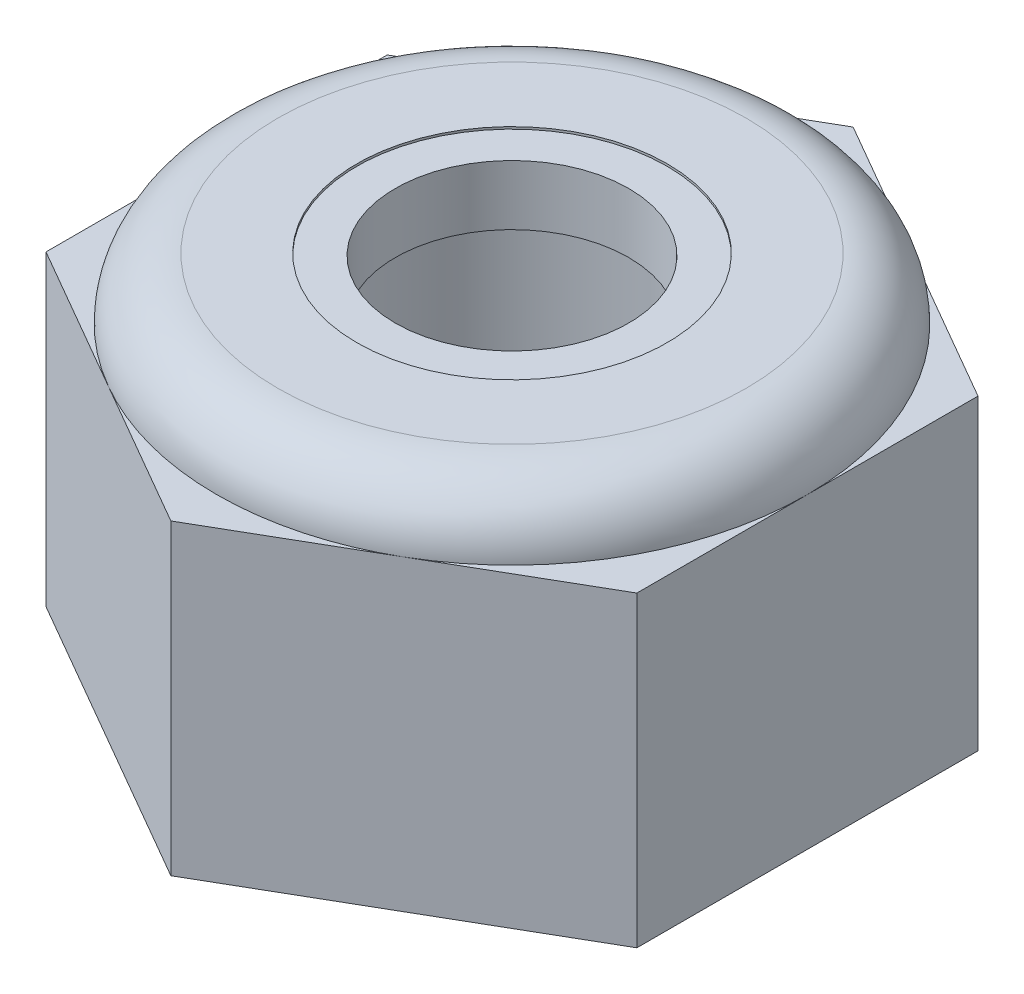
SolidWorks part; units mm, degrees
ref_plane "Front Plane" through (0, 0, 0) normal (0, 0, 1) x (1, 0, 0)
ref_plane "Top Plane" through (0, 0, 0) normal (0, 1, 0) x (1, 0, 0)
ref_plane "Right Plane" through (0, 0, 0) normal (1, 0, 0) x (0, 0, -1)
sketch "Sketch1" plane through (0, 0, 0) normal (0, 1, 0) x (1, 0, 0)
  line L1 (-4, -2.3094) -> (0, -4.6188)
  line L2 (0, -4.6188) -> (4, -2.3094)
  line L3 (4, -2.3094) -> (4, 2.3094)
  line L4 (4, 2.3094) -> (0, 4.6188)
  line L5 (0, 4.6188) -> (-4, 2.3094)
  line L6 (-4, 2.3094) -> (-4, -2.3094)
  line L7 (0, -55) -> (0, 55) construction
  circle A0 centre (0, 0) radius 4 construction
  dimension "D2" = 8
  dimension "D1" = 0
extrude "Boss-Extrude1" add sketch "Sketch1" along normal blind 4.16
sketch "Sketch3" plane through (0, 0, 0) normal (0, 0, 1) x (1, 0, 0)
  line L1 (3.17, 4.99) -> (0, 4.99)
  line L2 (0, 4.99) -> (0, 4.16)
  line L3 (0, 4.16) -> (4, 4.16)
  arc A0 (4, 4.16) -> (3.17, 4.99) centre (3.17, 4.16) ccw
  dimension "D2" = 0.83
  dimension "D1" = 0.83
revolve "Revolve1" add sketch "Sketch3" angle 360 about L2
hole_wizard "Tap Drill for M5x0.8 Tap1" positions "Sketch6" profile "Sketch7" hole size "M5x0.8" standard "ANSI Metric" end condition through all
sketch "Sketch6" plane through (0, 0, 0) normal (0, -1, 0) x (-1, 0, 0)
  point P0 (0, 0)
sketch "Sketch7" plane through (0, 0, 0) normal (1, 0, 0) x (0, 0, -1)
  line L0 (0, 0) -> (0, 4.99)
  line L1 (0, 4.99) -> (2.1, 4.99)
  line L2 (2.1, 4.99) -> (2.1, 0)
  line L5 (2.1, 0) -> (0, 0)
  line L11 (0, -6.35) -> (0, 107.95) construction
  dimension "Thru Hole Dia." = 4.2
  dimension "Thru Hole Depth" = 4.99
sketch "Sketch8" plane through (0, 0, 0) normal (0, 0, 1) x (1, 0, 0)
  line L0 (2.1, 4.96) -> (1.58, 4.96)
  line L2 (1.58, 4.96) -> (1.58, 4.15)
  line L4 (1.58, 4.15) -> (2.1, 4.15)
  line L6 (2.1, 4.15) -> (2.1, 4.96)
  line L8 (2.1, 4.99) -> (-2.1, 4.99) construction
  dimension "D1" = 0.52
  dimension "D2" = 0.81
  dimension "D3" = 0.03
ref_axis "Axis1" through (0, 4.99, 0) along (0, -1, 0)
revolve "Revolve2" add sketch "Sketch8" angle 360 about axis through (0, 4.99, 0) along (0, -1, 0)
